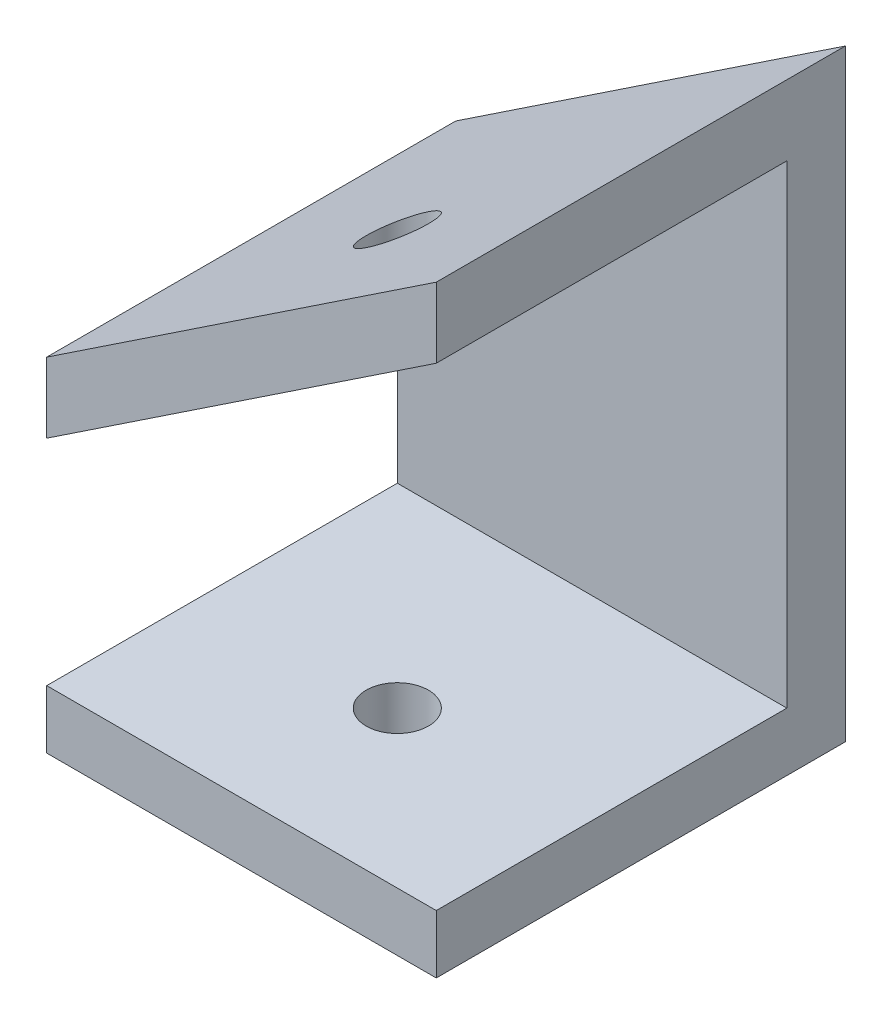
SolidWorks part; units mm, degrees
ref_plane "前视基准面" through (0, 0, 0) normal (0, 0, 1) x (1, 0, 0)
ref_plane "上视基准面" through (0, 0, 0) normal (0, 1, 0) x (1, 0, 0)
ref_plane "右视基准面" through (0, 0, 0) normal (1, 0, 0) x (0, 0, -1)
sketch "草图1" plane through (0, 0, 0) normal (0, 0, 1) x (1, 0, 0)
  line L1 (-7.6343, -2.9061) -> (-7.6343, 8.0939)
  line L2 (-7.6343, 8.0939) -> (7.3657, 8.0939) construction
  line L3 (7.3657, 8.0939) -> (7.3657, 18.0939) construction
  line L4 (-7.6343, 8.0939) -> (7.3657, 18.0939) construction
  line L5 (-7.6343, 8.0939) -> (12.3657, 21.4272)
  line L6 (12.3657, 2.0939) -> (12.3657, 21.4665) construction
  line L8 (12.3657, -5.9061) -> (-7.6343, -5.9061)
  line L9 (-7.6343, -2.9061) -> (-7.6343, -5.9061)
  line L10 (12.3657, 21.4272) -> (12.3657, -5.9061)
  point P1 (0, 0)
  dimension "D1" = 11
  dimension "D2" = 10
  dimension "15" = 15
  dimension "D3" = 5
extrude "凸台-拉伸1" add sketch "草图1" along normal blind 3
sketch "草图2" plane through (0, 0, 3) normal (0, 0, 1) x (1, 0, 0)
  line L0 (-7.6343, 8.0939) -> (12.3657, 21.4272)
  line L1 (-7.6343, 11.6994) -> (12.3657, 25.0327)
  line L2 (-7.6343, 8.0939) -> (-7.6343, -5.9061) construction
  line L3 (12.3657, -5.9061) -> (12.3657, 21.4272) construction
  line L4 (-7.6343, 8.0939) -> (-7.6343, 11.6994)
  line L5 (12.3657, 21.4272) -> (12.3657, 25.0327)
  line L6 (-7.6343, -5.9061) -> (-7.6343, -2.9061)
  line L7 (-7.6343, -2.9061) -> (12.3657, -2.9061)
  line L8 (12.3657, -2.9061) -> (12.3657, -5.9061)
  line L9 (12.3657, -5.9061) -> (-7.6343, -5.9061)
  dimension "D1" = 3
  dimension "D2" = 3
extrude "凸台-拉伸2" add sketch "草图2" along normal blind 18 and the other way blind 3
sketch "草图5" plane through (0, -5.9061, 0) normal (0, -1, 0) x (1, 0, 0)
  line L0 (-7.6343, 21) -> (12.3657, 21) construction
  circle A0 centre (2.3657, 13) radius 1.6
  dimension "D1" = 8
extrude "切除-拉伸1" cut sketch "草图5" against normal through all
